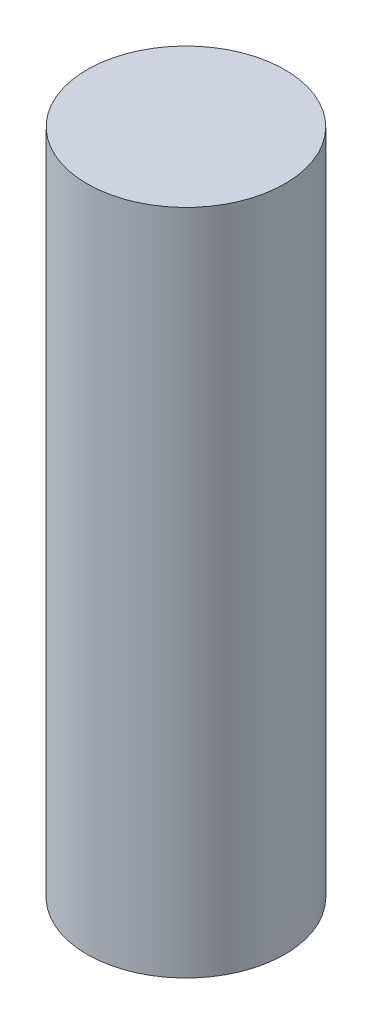
SolidWorks part; units mm, degrees
material "6061-T6 (SS)"
ref_plane "Front Plane" through (0, 0, 0) normal (0, 0, 1) x (1, 0, 0)
ref_plane "Top Plane" through (0, 0, 0) normal (0, 1, 0) x (1, 0, 0)
ref_plane "Right Plane" through (0, 0, 0) normal (1, 0, 0) x (0, 0, -1)
sketch "Sketch1" plane through (0, 0, 0) normal (0, 1, 0) x (1, 0, 0)
  circle A0 centre (0, 0) radius 4
  dimension "D1" = 8
extrude "Boss-Extrude1" add sketch "Sketch1" along normal mid plane 27
